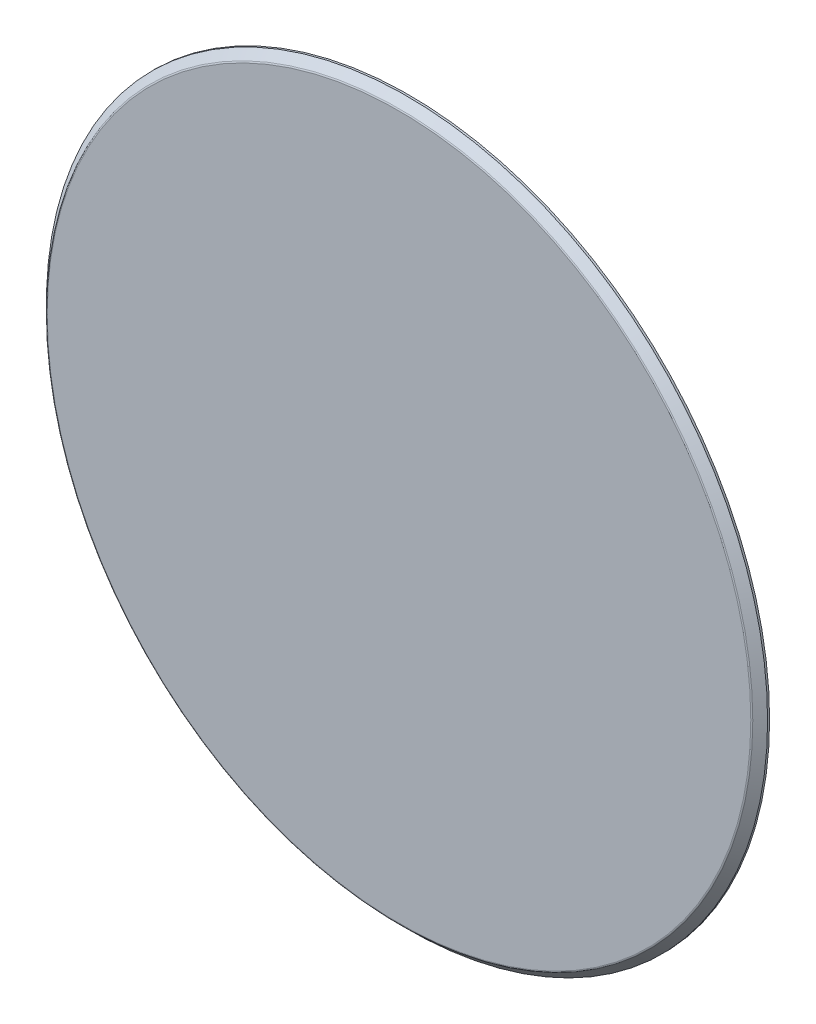
SolidWorks part; units mm, degrees
ref_plane "Front Plane" through (0, 0, 0) normal (0, 0, 1) x (1, 0, 0)
ref_plane "Top Plane" through (0, 0, 0) normal (0, 1, 0) x (1, 0, 0)
ref_plane "Right Plane" through (0, 0, 0) normal (1, 0, 0) x (0, 0, -1)
sketch "Sketch1" plane through (0, 0, 0) normal (0, 0, 1) x (1, 0, 0)
  circle A0 centre (0, 20) radius 18.0475
extrude "Boss-Extrude1" add sketch "Sketch1" along normal blind 0.5
chamfer "Chamfer1" distance 0.4 angle 45 1 edges at (18.0475, 20, 0.5)
fillet "Fillet1" radius 0.1 1 edges at (17.6475, 20, 0.5)
